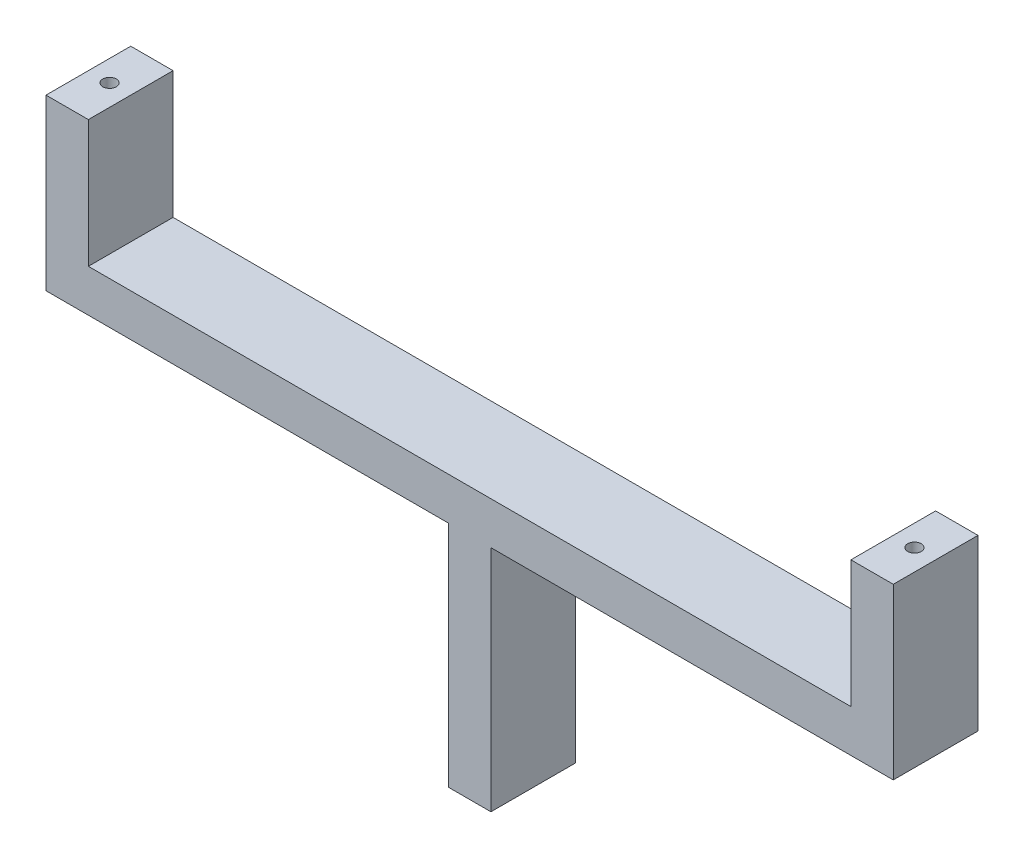
SolidWorks part; units mm, degrees
ref_plane "Alzado" through (0, 0, 0) normal (0, 0, 1) x (1, 0, 0)
ref_plane "Planta" through (0, 0, 0) normal (0, 1, 0) x (1, 0, 0)
ref_plane "Vista lateral" through (0, 0, 0) normal (1, 0, 0) x (0, 0, -1)
sketch "Croquis1" plane through (0, 0, 0) normal (0, 1, 0) x (1, 0, 0)
  line L1 (-50, -5) -> (50, -5)
  line L2 (-50, -5) -> (-50, 5)
  line L3 (-50, 5) -> (50, 5)
  line L4 (50, -5) -> (50, 5)
  line L5 (-50, -5) -> (50, 5) construction
  line L6 (-50, 5) -> (50, -5) construction
  point P0 (0, 0)
extrude "Saliente-Extruir1" add sketch "Croquis1" along normal blind 5
sketch "Croquis2" plane through (0, 5, 0) normal (0, 1, 0) x (1, 0, 0)
  line L0 (-50, -5) -> (50, -5) construction
  line L1 (-50, -5) -> (-45, -5)
  line L2 (-50, -5) -> (-50, 5)
  line L3 (-50, 5) -> (-45, 5)
  line L4 (-45, -5) -> (-45, 5)
  line L5 (50, 5) -> (45, 5)
  line L6 (50, 5) -> (50, -5)
  line L7 (50, -5) -> (45, -5)
  line L8 (45, 5) -> (45, -5)
extrude "Saliente-Extruir2" add sketch "Croquis2" along normal blind 15
sketch "Croquis3" plane through (0, 20, 0) normal (0, 1, 0) x (1, 0, 0)
  circle A0 centre (-47.5, 0) radius 0.8
  circle A1 centre (47.5, 0) radius 0.8
  dimension "D1" = 1.6
extrude "Cortar-Extruir1" cut sketch "Croquis3" against normal blind 5
sketch "Croquis4" plane through (0, 0, 0) normal (0, -1, 0) x (1, 0, 0)
  line L0 (50, -5) -> (-50, -5) construction
  line L1 (-2.5146, 5) -> (2.5146, 5)
  line L2 (-2.5146, 5) -> (-2.5146, -5)
  line L3 (-2.5146, -5) -> (2.5146, -5)
  line L4 (2.5146, 5) -> (2.5146, -5)
  line L5 (-2.5146, 5) -> (2.5146, -5) construction
  line L6 (-2.5146, -5) -> (2.5146, 5) construction
  point P0 (0, 0)
extrude "Saliente-Extruir3" add sketch "Croquis4" along normal blind 27
sketch "Croquis5" plane through (0, -27, 0) normal (0, -1, 0) x (1, 0, 0)
  circle A0 centre (0, 0) radius 0.8
extrude "Cortar-Extruir2" cut sketch "Croquis5" against normal blind 10
